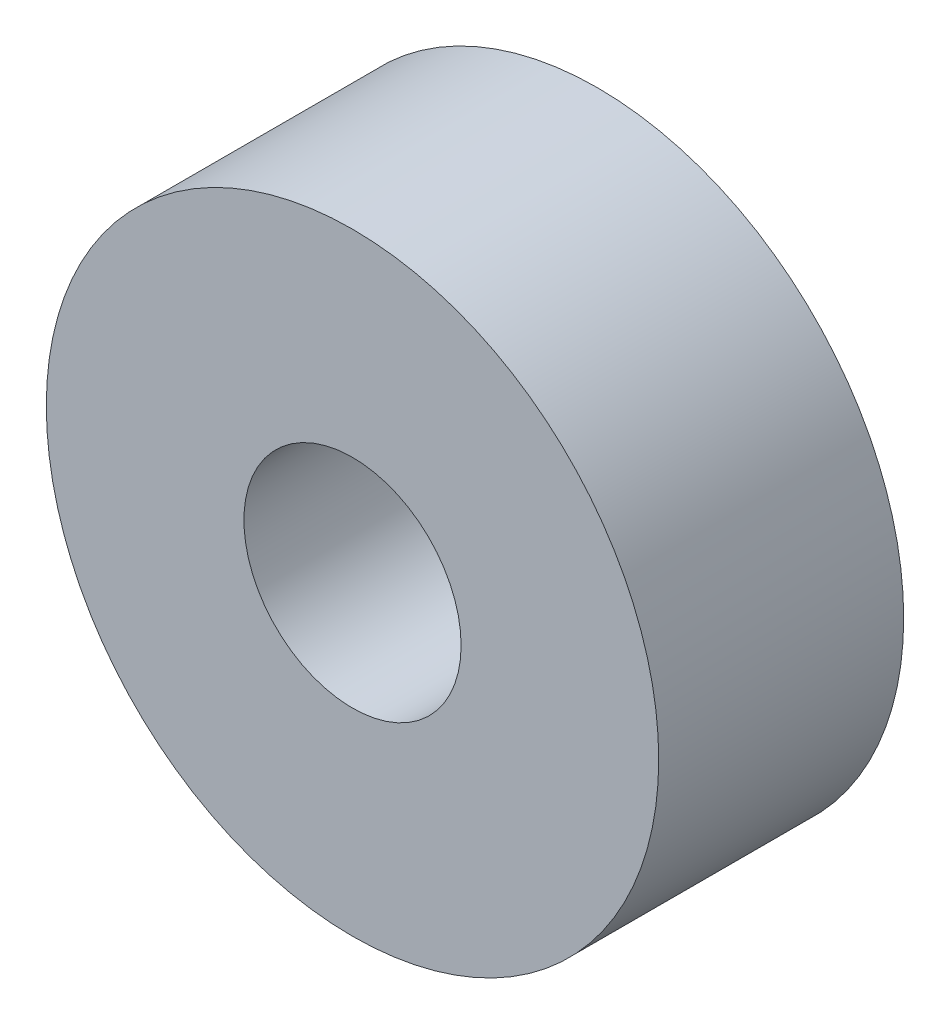
SolidWorks part; units mm, degrees
material "SS 304"
ref_plane "Front Plane" through (0, 0, 0) normal (0, 0, 1) x (1, 0, 0)
ref_plane "Top Plane" through (0, 0, 0) normal (0, 1, 0) x (1, 0, 0)
ref_plane "Right Plane" through (0, 0, 0) normal (1, 0, 0) x (0, 0, -1)
sketch "Sketch1" plane through (0, 0, 0) normal (0, 0, 1) x (1, 0, 0)
  circle A0 centre (0, 0) radius 9.525
  dimension "D1" = 19.05
extrude "Boss-Extrude1" add sketch "Sketch1" along normal mid plane 7.62
sketch "Sketch2" plane through (0, 0, 3.81) normal (0, 0, 1) x (1, 0, 0)
  circle A0 centre (0, 0) radius 3.3782
  dimension "D1" = 6.7564
extrude "Cut-Extrude1" cut sketch "Sketch2" against normal up to next
